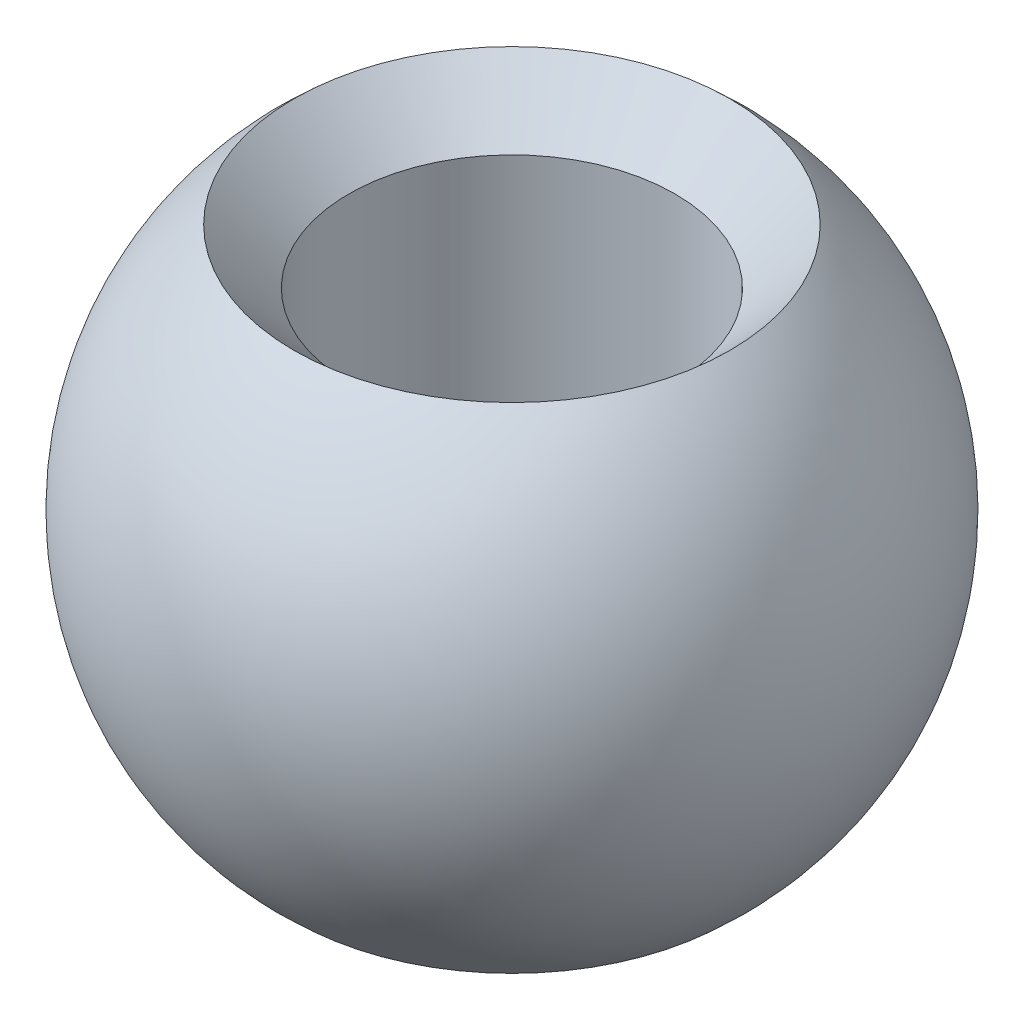
SolidWorks part; units mm, degrees
ref_plane "Front Plane" through (0, 0, 0) normal (0, 0, 1) x (1, 0, 0)
ref_plane "Top Plane" through (0, 0, 0) normal (0, 1, 0) x (1, 0, 0)
ref_plane "Right Plane" through (0, 0, 0) normal (1, 0, 0) x (0, 0, -1)
sketch "Sketch1" plane through (0, 0, 0) normal (0, 0, 1) x (1, 0, 0)
  line L0 (0, -8.4013) -> (0, 11.8735) construction
  line L1 (-6.4308, 4.5) -> (-3.9686, 4.5)
  line L2 (-7.5232, 0) -> (10.7456, 0) construction
  line L3 (-3.9686, -4.5) -> (-2.9686, -4.5)
  line L5 (-3.9686, 4.5) -> (-2.9686, 3.5)
  line L6 (-2.9686, 3.5) -> (-2.9686, -4.5)
  arc A0 (-3.9686, 4.5) -> (-3.9686, -4.5) centre (0, 0) ccw
  dimension "D1" = 12
  dimension "D2" = 4.5
  dimension "D4" = 45
revolve "Revolve4" add sketch "Sketch1" angle 360 about L0
